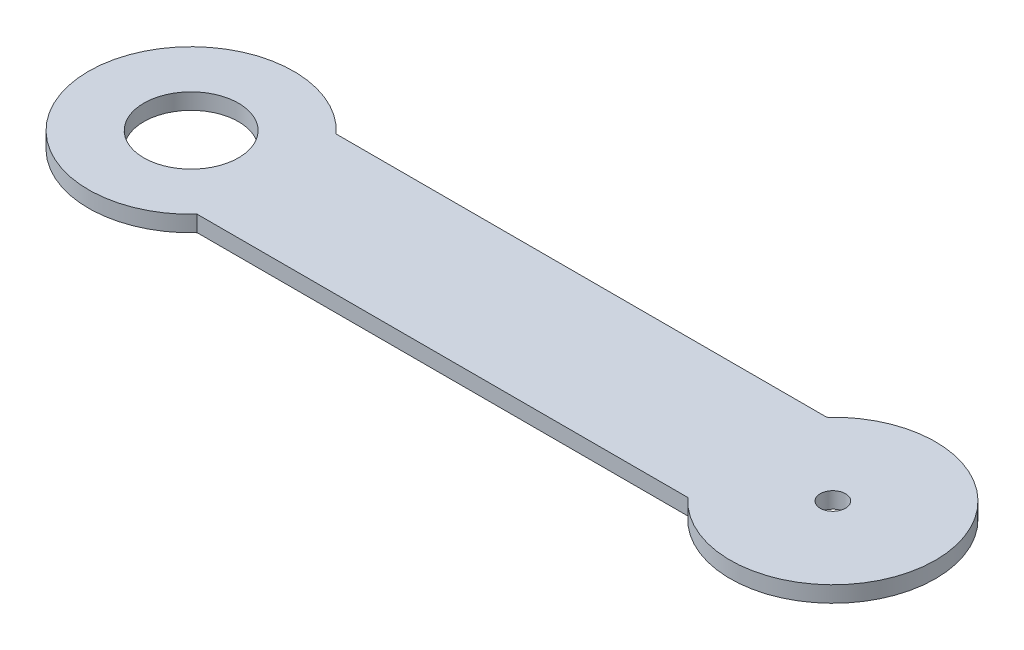
SolidWorks part; units mm, degrees
ref_plane "Front Plane" through (0, 0, 0) normal (0, 0, 1) x (1, 0, 0)
ref_plane "Top Plane" through (0, 0, 0) normal (0, 1, 0) x (1, 0, 0)
ref_plane "Right Plane" through (0, 0, 0) normal (1, 0, 0) x (0, 0, -1)
sketch "Sketch1" plane through (0, 0, 0) normal (0, 1, 0) x (1, 0, 0)
  line L0 (-50.8, 0) -> (50.8, 0) construction
  line L1 (-38.836, 11) -> (38.836, 11)
  line L2 (-38.836, -11) -> (38.836, -11)
  arc A2 (-38.836, 11) -> (-38.836, -11) centre (-50.8, 0) ccw
  arc A3 (38.836, -11) -> (38.836, 11) centre (50.8, 0) ccw
  point P3 (0, 0)
  dimension "D4" = 32.5046
  dimension "D5" = 32.5046
  dimension "D1" = 22
  dimension "D2" = 101.6
  dimension "D3" = 50.8
extrude "Boss-Extrude1" add sketch "Sketch1" along normal blind 2.54
sketch "Sketch2" plane through (0, 2.54, 0) normal (0, 1, 0) x (1, 0, 0)
  circle A0 centre (-50.8, 0) radius 7.5
  circle A1 centre (50.8, 0) radius 2
  dimension "D1" = 15
  dimension "D4" = 4
  dimension "D2" = 50.8
  dimension "D3" = 50.8
extrude "Cut-Extrude1" cut sketch "Sketch2" against normal blind 2.54
